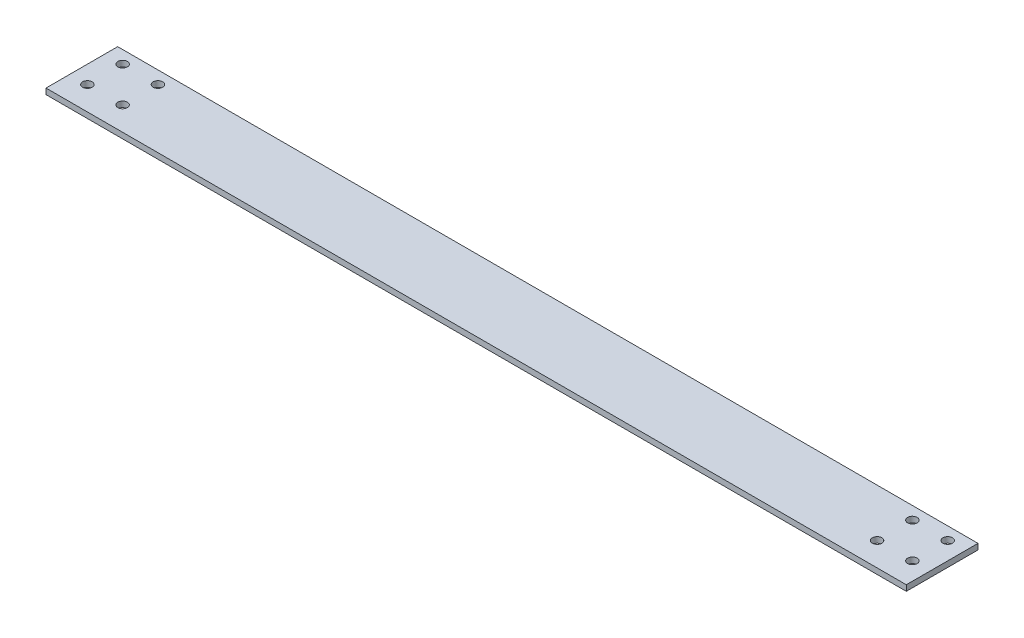
SolidWorks part; units mm, degrees
ref_plane "Front Plane" through (0, 0, 0) normal (0, 0, 1) x (1, 0, 0)
ref_plane "Top Plane" through (0, 0, 0) normal (0, 1, 0) x (1, 0, 0)
ref_plane "Right Plane" through (0, 0, 0) normal (1, 0, 0) x (0, 0, -1)
sketch "Sketch1" plane through (0, 0, 0) normal (0, 1, 0) x (1, 0, 0)
  line L0 (0, 0) -> (609.6, 0)
  line L1 (0, 0) -> (0, 7)
  line L2 (0, 7) -> (609.6, 7)
  line L3 (609.6, 7) -> (609.6, 0)
  line L4 (0, 0) -> (0, 50.8)
  line L5 (0, 50.8) -> (609.6, 50.8)
  line L6 (609.6, 50.8) -> (609.6, 0)
  line L7 (0, 50.8) -> (50, 50.8) construction
  line L8 (50, 50.8) -> (50, 0) construction
  line L9 (50, 50.8) -> (25, 50.8) construction
  line L10 (0, 0) -> (25, 0) construction
  line L11 (25, 50.8) -> (25, 29.3) construction
  line L12 (25, 41.8) -> (25, 29.3) construction
  line L13 (25, 29.3) -> (25, 16.8) construction
  line L14 (12.5, 16.8) -> (37.5, 16.8) construction
  line L15 (12.5, 41.8) -> (37.5, 41.8) construction
  line L16 (304.8, 50.8) -> (304.8, 0) construction
  line L17 (597.1, 41.8) -> (572.1, 41.8) construction
  line L18 (597.1, 16.8) -> (572.1, 16.8) construction
  line L19 (584.6, 29.3) -> (584.6, 16.8) construction
  line L20 (584.6, 41.8) -> (584.6, 29.3) construction
  line L21 (584.6, 50.8) -> (584.6, 29.3) construction
  line L22 (609.6, 0) -> (584.6, 0) construction
  line L23 (559.6, 50.8) -> (584.6, 50.8) construction
  line L24 (559.6, 50.8) -> (559.6, 0) construction
  line L25 (609.6, 50.8) -> (559.6, 50.8) construction
  line L26 (609.6, 0) -> (609.6, 50.8)
  line L27 (609.6, 0) -> (609.6, 7)
  line L32 (609.6, 0) -> (609.6, 50.8)
  line L33 (609.6, 0) -> (609.6, 7)
  point P21 (565.8092, 87.8785)
  point P33 (0, 0)
extrude "Boss-Extrude1" add sketch "Sketch1" along normal blind 4.064 contours L6 L5 L4 L2 | L3 L2 L1 L0
hole_wizard "1/4 Clearance Hole1" positions "Sketch2" profile "Sketch3" hole size "1/4" standard "ANSI Inch" end condition through all
sketch "Sketch2" plane through (0, 0, 0) normal (0, -1, 0) x (-1, 0, 0)
  point P0 (-12.5, 41.8)
  point P5 (-37.5, 41.8)
  point P8 (-37.5, 16.8)
  point P11 (-12.5, 16.8)
  point P14 (-572.1, 41.8)
  point P17 (-597.1, 41.8)
  point P20 (-597.1, 16.8)
  point P23 (-572.1, 16.8)
sketch "Sketch3" plane through (12.5, 0, -41.8) normal (1, 0, 0) x (0, 0, -1)
  line L0 (0, 0) -> (0, 4.064)
  line L1 (0, 4.064) -> (3.3782, 4.064)
  line L2 (3.3782, 4.064) -> (3.3782, 0)
  line L5 (3.3782, 0) -> (0, 0)
  line L11 (0, -6.35) -> (0, 107.95) construction
  dimension "Thru Hole Dia." = 6.7564
  dimension "Thru Hole Depth" = 4.064
